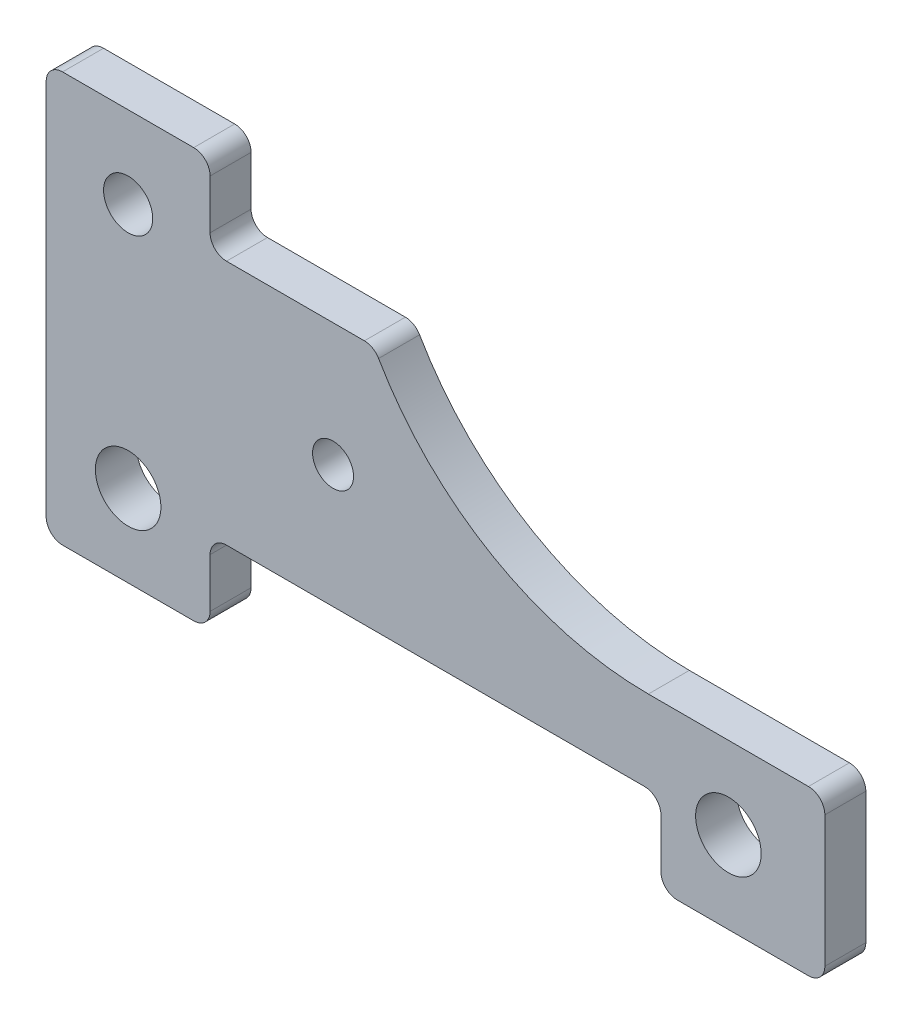
SolidWorks part; units mm, degrees
ref_plane "Front Plane" through (0, 0, 0) normal (0, 0, 1) x (1, 0, 0)
ref_plane "Top Plane" through (0, 0, 0) normal (0, 1, 0) x (1, 0, 0)
ref_plane "Right Plane" through (0, 0, 0) normal (1, 0, 0) x (0, 0, -1)
sketch "Sketch6" plane through (0, 0, 0) normal (0, 0, 1) x (1, 0, 0)
  line L0 (20, 0) -> (180, 0)
  line L1 (200, 20) -> (200, 80)
  line L2 (220, 100) -> (730, 100)
  line L3 (750, 80) -> (750, 20)
  line L4 (770, 0) -> (930, 0)
  line L5 (950, 20) -> (950, 180)
  line L6 (0, 20) -> (0, 480)
  line L7 (20, 500) -> (180, 500)
  line L8 (200, 480) -> (200, 420)
  line L9 (220, 400) -> (388.2538, 400)
  line L10 (930, 200) -> (734.664, 200)
  arc A0 (734.664, 200) -> (405.5744, 390) centre (734.664, 580) cw
  arc A1 (0, 20) -> (20, 0) centre (20, 20) ccw
  arc A2 (180, 0) -> (200, 20) centre (180, 20) ccw
  arc A3 (200, 80) -> (220, 100) centre (220, 80) cw
  arc A4 (750, 80) -> (730, 100) centre (730, 80) ccw
  arc A5 (750, 20) -> (770, 0) centre (770, 20) ccw
  arc A6 (930, 0) -> (950, 20) centre (930, 20) ccw
  arc A7 (950, 180) -> (930, 200) centre (930, 180) ccw
  arc A8 (405.5744, 390) -> (388.2538, 400) centre (388.2538, 380) ccw
  arc A9 (220, 400) -> (200, 420) centre (220, 420) cw
  arc A10 (200, 480) -> (180, 500) centre (180, 480) ccw
  arc A11 (0, 480) -> (20, 500) centre (20, 480) cw
  point P8 (100, 0)
  point P9 (850, 0)
  point P18 (0, 0)
  point P21 (200, 0)
  point P24 (200, 100)
  point P27 (750, 100)
  point P32 (950, 0)
  point P35 (950, 200)
  point P38 (400, 400)
  point P41 (200, 400)
  point P44 (200, 500)
  point P47 (0, 500)
  dimension "D8" = 380
  dimension "D9" = 20
  dimension "D1" = 750
  dimension "D2" = 550
  dimension "D3" = 100
  dimension "D4" = 200
  dimension "D5" = 100
  dimension "D6" = 200
  dimension "D7" = 200
extrude "Boss-Extrude4" add sketch "Sketch6" along normal mid plane 50
sketch "Sketch8" plane through (0, 0, 25) normal (0, 0, 1) x (1, 0, 0)
  line L0 (20, 0) -> (180, 0) construction
  line L1 (100, 400) -> (100, 250)
  line L2 (100, 250) -> (350, 250) construction
  circle A0 centre (100, 400) radius 30
  circle A1 centre (100, 100) radius 40
  circle A2 centre (350, 250) radius 25
  circle A3 centre (832.332, 100) radius 40
  point P6 (100, 0)
  point P12 (0, 0)
  dimension "D1" = 60
  dimension "D2" = 80
  dimension "D5" = 0
  dimension "D7" = 50
  dimension "D8" = 80
  dimension "D3" = 300
  dimension "D4" = 100
  dimension "D6" = 150
extrude "Cut-Extrude2" cut sketch "Sketch8" against normal through all
